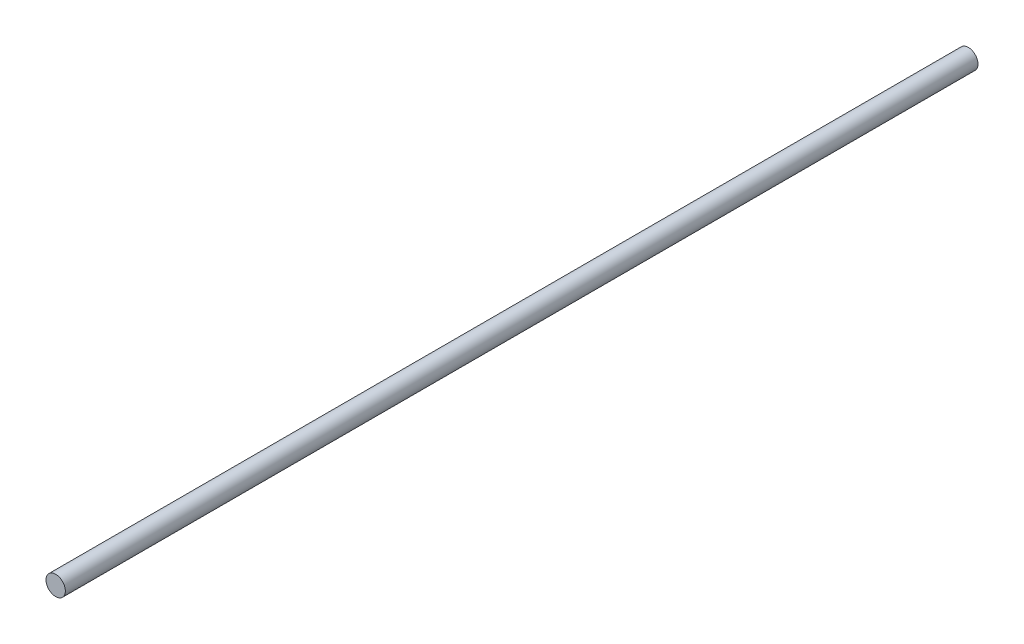
SolidWorks part; units mm, degrees
material "201 Annealed Stainless Steel (SS)"
ref_plane "Front Plane" through (0, 0, 0) normal (0, 0, 1) x (1, 0, 0)
ref_plane "Top Plane" through (0, 0, 0) normal (0, 1, 0) x (1, 0, 0)
ref_plane "Right Plane" through (0, 0, 0) normal (1, 0, 0) x (0, 0, -1)
sketch "Sketch1" plane through (0, 0, 0) normal (0, 0, 1) x (1, 0, 0)
  circle A0 centre (0, 0) radius 3
  dimension "D1" = 6
extrude "Boss-Extrude1" add sketch "Sketch1" along normal mid plane 282.5
